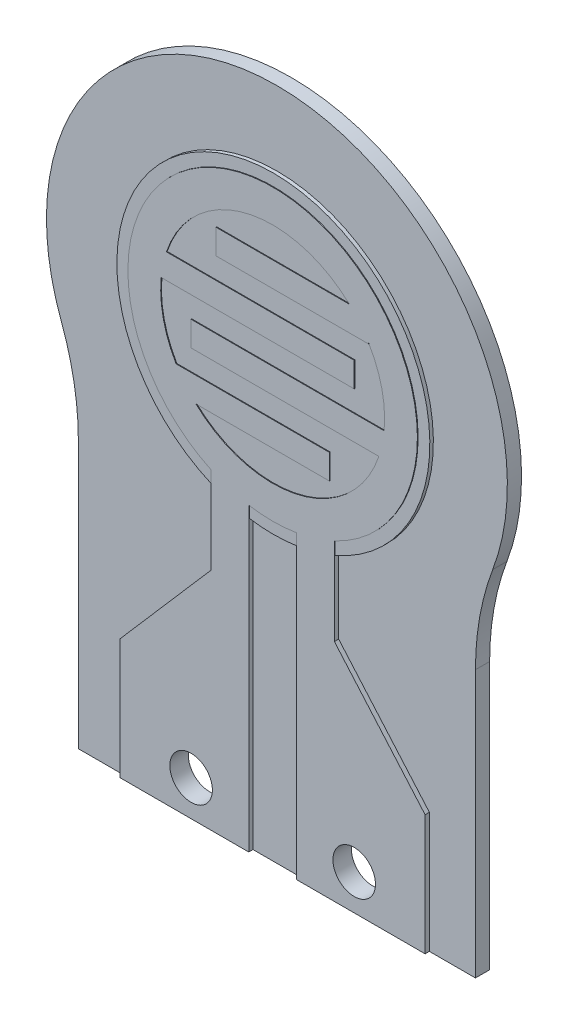
SolidWorks part; units mm, degrees
ref_plane "Front" through (0, 0, 0) normal (0, 0, 1) x (1, 0, 0)
ref_plane "Top" through (0, 0, 0) normal (0, 1, 0) x (1, 0, 0)
ref_plane "Right" through (0, 0, 0) normal (1, 0, 0) x (0, 0, -1)
sketch "Sketch1" plane through (0, 0, 0) normal (0, 0, 1) x (1, 0, 0)
  line L0 (0, 0) -> (0, -6.25) construction
  line L1 (-2.8, -6.25) -> (2.8, -6.25)
  line L2 (2.8, -6.25) -> (2.8, -2.4846)
  line L3 (0, 3.25) -> (0, 0) construction
  line L4 (-2.8, -6.25) -> (-2.8, -2.4846)
  arc A0 (3.0436, -1.1399) -> (-3.0436, -1.1399) centre (0, 0) ccw
  arc A1 (2.8, -2.4846) -> (3.0436, -1.1399) centre (6.6343, -2.4846) cw
  arc A2 (-2.8, -2.4846) -> (-3.0436, -1.1399) centre (-6.6343, -2.4846) ccw
  point P12 (2.0943, -2.4853)
  point P13 (2.0814, -3.315)
  point P14 (2.3968, -3.7147)
  point P15 (2.8, -2.4846)
  point P16 (0, 3.25)
  dimension "D1" = 6.5
  dimension "D2" = 5.6
  dimension "D3" = 9.5
extrude "Boss-Extrude1" add sketch "Sketch1" along normal blind 0.2
sketch "Sketch2" plane through (0, 0, 0) normal (0, 0, -1) x (-1, 0, 0)
  circle A0 centre (0, 0) radius 2.2068
extrude "Boss-Extrude2" add sketch "Sketch2" against normal blind 0.25
sketch "Sketch3" plane through (0, 0, 0.2) normal (0, 0, 1) x (1, 0, 0)
  line L0 (0.8707, -1.8464) -> (0.8707, -3.0753)
  line L1 (-0.8, 1.15) -> (1.0819, 1.15)
  line L2 (-0.8, 1.15) -> (-0.8, 0.8)
  line L3 (-0.8, 0.8) -> (1.3551, 0.8)
  line L4 (1.3551, 0.8104) -> (1.3551, 0.8)
  line L5 (1.15, 0.5) -> (-1.4977, 0.5)
  line L6 (1.15, 0.5) -> (1.15, 0.15)
  line L7 (1.15, 0.15) -> (-1.5718, 0.15)
  line L9 (-1.15, -0.15) -> (1.5718, -0.15)
  line L10 (-1.15, -0.15) -> (-1.15, -0.5)
  line L11 (-1.15, -0.5) -> (1.4977, -0.5)
  line L13 (0.8, -0.8) -> (-1.3613, -0.8)
  line L14 (0.8, -0.8) -> (0.8, -1.15)
  line L15 (0.8, -1.15) -> (-1.0819, -1.15)
  line L17 (-2.8, -6.25) -> (2.8, -6.25) construction
  line L18 (0.3371, -2.0134) -> (0.3371, -6.25)
  line L19 (0.3371, -6.25) -> (2.15, -6.25)
  line L20 (2.15, -6.25) -> (2.15, -4.5508)
  line L22 (0, 0) -> (0, -6.25) construction
  line L23 (0.8707, -3.0753) -> (2.15, -4.5508)
  line L24 (-2.15, -6.25) -> (-2.15, -4.5508)
  line L25 (-0.8707, -3.0753) -> (-2.15, -4.5508)
  line L26 (-0.8707, -1.8464) -> (-0.8707, -3.0753)
  line L27 (-0.3371, -2.0134) -> (-0.3371, -6.25)
  line L28 (-2.15, -6.25) -> (-0.3371, -6.25)
  arc A0 (0.8707, -1.8464) -> (-0.8707, -1.8464) centre (0, 0) ccw
  arc A1 (1.5718, -0.15) -> (1.3551, 0.8104) centre (0, 0) ccw
  arc A2 (1.0819, 1.15) -> (-1.4977, 0.5) centre (0, 0) ccw
  arc A3 (-1.5718, 0.15) -> (-1.3613, -0.8) centre (0, 0) ccw
  arc A4 (-1.0819, -1.15) -> (1.4977, -0.5) centre (0, 0) ccw
  arc A5 (-0.3371, -2.0134) -> (0.3371, -2.0134) centre (0, 0) ccw
  point P1 (1.1073, -1.7151)
  point P24 (0.8707, -3.0753)
  point P28 (2.15, -4.5508)
  dimension "D1" = 1.15
  dimension "D2" = 1.15
  dimension "D3" = 0.8
  dimension "D4" = 0.8
  dimension "D5" = 0.8
  dimension "D6" = 0.8
  dimension "D7" = 0.15
  dimension "D8" = 0.15
  dimension "D9" = 0.35
  dimension "D10" = 4.3
extrude "Boss-Extrude3" add sketch "Sketch3" along normal blind 0.06
sketch "Sketch5" plane through (0, 0, 0.26) normal (0, 0, 1) x (1, 0, 0)
  line L0 (0, 0) -> (0, -3.7187) construction
  line L1 (0.3371, -6.25) -> (2.15, -6.25) construction
  circle A0 centre (-1.15, -5.75) radius 0.3
  circle A3 centre (1.15, -5.75) radius 0.3
  point P6 (-0.9731, -5.0978)
  dimension "D1" = 0.6
  dimension "D2" = 2.3
  dimension "D3" = 0.5
extrude "Cut-Extrude1" cut sketch "Sketch5" against normal through all
